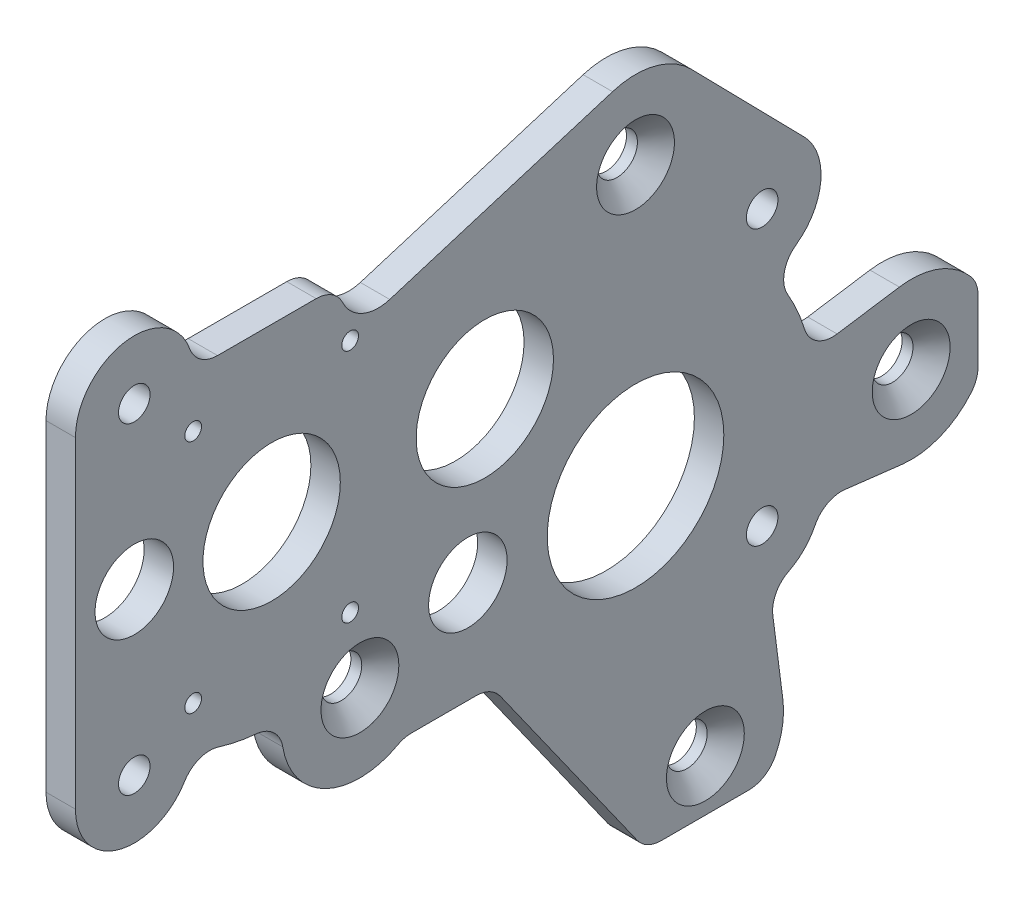
SolidWorks part; units mm, degrees
material "5052-H32"
ref_plane "Front Plane" through (0, 0, 0) normal (0, 0, 1) x (1, 0, 0)
ref_plane "Top Plane" through (0, 0, 0) normal (0, 1, 0) x (1, 0, 0)
ref_plane "Right Plane" through (0, 0, 0) normal (1, 0, 0) x (0, 0, -1)
sketch "Sketch1" plane through (0, 0, 0) normal (1, 0, 0) x (0, 0, -1)
  line L1 (0, 0) -> (146.05, 0)
  line L2 (0, 0) -> (0, 127)
  line L3 (0, 127) -> (146.05, 127)
  line L4 (146.05, 0) -> (146.05, 127)
  dimension "D1" = 146.05
  dimension "D2" = 127
extrude "Boss-Extrude2" add sketch "Sketch1" along normal blind 4.7625
sketch "Sketch2" plane through (4.7625, 0, 0) normal (1, 0, 0) x (0, 0, -1)
  line L0 (66.2432, 127) -> (66.2432, 0) construction
  line L1 (0, 127) -> (0, 0) construction
  line L2 (66.2432, 76.2) -> (90.6336, 51.8096) construction
  line L3 (0, 0) -> (146.05, 0) construction
  line L4 (146.05, 127) -> (0, 127) construction
  circle A0 centre (31.75, 76.2) radius 25.5016 construction
  circle A1 centre (90.6336, 51.8096) radius 8.9916 construction
  circle A2 centre (90.6336, 51.8096) radius 14.2875
  circle A3 centre (31.75, 76.2) radius 11.1125
  circle A4 centre (66.2432, 76.2) radius 25.5016 construction
  circle A5 centre (66.2432, 76.2) radius 8.9916 construction
  circle A6 centre (66.2432, 76.2) radius 11.1125
  dimension "D1" = 51.0032
  dimension "D2" = 17.9832
  dimension "D4" = 28.575
  dimension "D5" = 22.225
  dimension "D6" = 45
  dimension "D3" = 51.0032
  dimension "D7" = 17.9832
  dimension "D8" = 22.225
  dimension "D9" = 31.75
  dimension "D10" = 76.2
extrude "Cut-Extrude1" cut sketch "Sketch2" against normal through all
hole_wizard "CSK for M6 Flat Head Machine Screw1" positions "Sketch3" profile "Sketch4" countersink size "M6" standard "ANSI Metric" end condition through all
sketch "Sketch3" plane through (4.7625, 0, 0) normal (1, 0, 0) x (0, 0, -1)
  circle A1 centre (46.0336, 45.8096) radius 2.5 construction
  circle A2 centre (101.9336, 8.3096) radius 2.5 construction
  circle A3 centre (90.6336, 96.8096) radius 2.5 construction
  circle A4 centre (135.2336, 45.8096) radius 2.5 construction
  circle A5 centre (46.0336, 45.8096) radius 2.5
  circle A6 centre (101.9336, 8.3096) radius 2.5
  circle A7 centre (90.6336, 96.8096) radius 2.5
  circle A8 centre (135.2336, 45.8096) radius 2.5
  point P58 (101.9336, 8.3096)
  point P61 (46.0336, 45.8096)
  point P64 (135.2336, 45.8096)
  point P67 (90.6336, 96.8096)
sketch "Sketch4" plane through (4.7625, 96.8096, -90.6336) normal (0, 1, 0) x (0, 0, -1)
  line L0 (0, 0) -> (0, 4.7625)
  line L1 (0, 4.7625) -> (3.3, 4.7625)
  line L2 (3.3, 4.7625) -> (3.3, 3)
  line L3 (3.3, 3) -> (6.3, 0)
  line L5 (6.3, 0) -> (0, 0)
  line L6 (-3.3, 3) -> (-6.3, 0) construction
  line L11 (0, -6.35) -> (0, 107.95) construction
  dimension "Thru Hole Dia." = 6.6
  dimension "Thru Hole Depth" = 4.7625
  dimension "Near C'Sink Dia." = 12.6
  dimension "Near C'Sink Angle" = 90
hole_wizard "#10 Clearance Hole2" positions "Sketch5" profile "Sketch6" hole size "#10" standard "ANSI Inch" end condition through all
sketch "Sketch5" plane through (4.7625, 0, 0) normal (1, 0, 0) x (0, 0, -1)
  line L2 (9.525, 103.8796) -> (9.525, 51.8096)
  line L6 (0, 127) -> (0, 0) construction
  line L8 (111.125, 35.9346) -> (111.125, 80.3846)
  circle A2 centre (90.6336, 51.8096) radius 14.2875 construction
  point P423 (9.525, 103.8796)
  point P426 (111.125, 80.3846)
  point P432 (9.525, 51.8096)
  point P470 (111.125, 35.9346)
  dimension "D1" = 52.07
  dimension "D2" = 44.45
  dimension "D3" = 101.6
  dimension "D4" = 9.525
  dimension "D5" = 0
  dimension "D6" = 15.875
sketch "Sketch6" plane through (4.7625, 35.9346, -111.125) normal (0, 1, 0) x (0, 0, -1)
  line L0 (0, 0) -> (0, 4.7625)
  line L1 (0, 4.7625) -> (2.5527, 4.7625)
  line L2 (2.5527, 4.7625) -> (2.5527, 0)
  line L5 (2.5527, 0) -> (0, 0)
  line L11 (0, -6.35) -> (0, 107.95) construction
  dimension "Thru Hole Dia." = 5.1054
  dimension "Thru Hole Depth" = 4.7625
fillet "Fillet2" radius 9.525 4 edges at (2.3813, 127, 0) (2.3813, 0, 0) (2.3813, 0, -146.05) (2.3813, 127, -146.05)
hole_wizard "#6-32 Tapped Hole1" positions "Sketch9" profile "Sketch10" tap size "#6-32" standard "ANSI Inch" end condition through all
sketch "Sketch9" plane through (0, 0, 0) normal (-1, 0, 0) x (0, 0, 1)
  line L2 (-44.45, 57.15) -> (-19.05, 57.15)
  line L3 (-44.45, 57.15) -> (-44.45, 95.25)
  line L4 (-44.45, 95.25) -> (-19.05, 95.25)
  line L5 (-19.05, 57.15) -> (-19.05, 95.25)
  line L6 (-44.45, 57.15) -> (-19.05, 95.25) construction
  line L7 (-44.45, 95.25) -> (-19.05, 57.15) construction
  point P17 (-31.75, 76.2)
  point P130 (-19.05, 57.15)
  point P133 (-44.45, 57.15)
  point P136 (-44.45, 95.25)
  point P139 (-19.05, 95.25)
  dimension "D1" = 38.1
  dimension "D2" = 25.4
sketch "Sketch10" plane through (0, 76.2, -31.75) normal (0, 1, 0) x (0, 0, 1)
  line L0 (0, 0) -> (0, 4.7625)
  line L1 (0, 4.7625) -> (1.3525, 4.7625)
  line L2 (1.3525, 4.7625) -> (1.3525, 0)
  line L5 (1.3525, 0) -> (0, 0)
  line L11 (0, -6.35) -> (0, 107.95) construction
  dimension "Thru Tap Drill Dia." = 2.7051
  dimension "Thru Tap Drill Depth" = 4.7625
cosmetic thread "Hole Thread1" parameters "D2"=3.5052
cosmetic thread "Hole Thread2" parameters "D2"=3.5052
cosmetic thread "Hole Thread3" parameters "D2"=3.5052
cosmetic thread "Hole Thread4" parameters "D2"=3.5052
sketch "Sketch11" plane through (4.7625, 0, 0) normal (1, 0, 0) x (0, 0, -1)
  line L0 (19.05, 103.8796) -> (42.6466, 103.8796)
  line L3 (50.8637, 97.8103) -> (86.9141, 108.9004)
  line L4 (117.9243, 87.0551) -> (99.6636, 105.6685)
  line L5 (90.6336, 51.8096) -> (133.328, 58.3153) construction
  line L6 (118.8825, 56.1141) -> (133.328, 58.3153)
  line L7 (111.125, 35.9346) -> (133.7413, 33.2479) construction
  line L9 (111.125, 35.9346) -> (114.4796, 9.928) construction
  line L10 (112.3435, 26.4879) -> (114.4796, 9.928)
  line L14 (91.6113, 0.9971) -> (67.3166, 35.2915)
  line L16 (67.3166, 35.2915) -> (53.0615, 35.2915)
  line L17 (0, 117.475) -> (0, 9.525) construction
  line L18 (0, 51.8096) -> (0, 0)
  line L20 (111.4715, 0) -> (146.05, 0)
  line L21 (9.525, 0) -> (136.525, 0) construction
  line L23 (133.7413, 33.2479) -> (120.5835, 34.811)
  line L24 (146.05, 39.2501) -> (146.05, 0)
  line L25 (146.05, 9.525) -> (146.05, 117.475) construction
  line L27 (146.05, 52.3692) -> (146.05, 127)
  line L28 (146.05, 127) -> (0, 127)
  line L29 (0, 127) -> (0, 103.8796)
  line L30 (136.525, 127) -> (9.525, 127) construction
  line L31 (0, 0) -> (92.3956, 0)
  circle A9 centre (90.6336, 51.8096) radius 28.575 construction
  arc A17 (146.05, 52.3692) -> (146.05, 39.2501) centre (135.2336, 45.8096) ccw construction
  circle A25 centre (90.6336, 96.8096) radius 12.65 construction
  arc A27 (111.4715, 0) -> (92.3956, 0) centre (101.9336, 8.3096) ccw construction
  circle A32 centre (9.525, 77.8446) radius 2.8067 construction
  circle A33 centre (63.5, 51.8096) radius 2.8067 construction
  circle A34 centre (125.057, 77.8446) radius 2.8067 construction
  circle A35 centre (48.9966, 103.8796) radius 2.8067 construction
  circle A36 centre (9.525, 77.8446) radius 2.8067 construction
  circle A37 centre (63.5, 51.8096) radius 2.8067 construction
  circle A38 centre (125.057, 77.8446) radius 2.8067 construction
  circle A39 centre (48.9966, 103.8796) radius 2.8067 construction
  circle A40 centre (9.525, 77.8446) radius 6.35
  arc A41 (42.6466, 103.8796) -> (50.8637, 97.8103) centre (48.9966, 103.8796) ccw
  circle A42 centre (63.5, 51.8096) radius 6.35
  circle A44 centre (46.0336, 45.8096) radius 12.65 construction
  circle A45 centre (31.75, 76.2) radius 28.575 construction
  circle A47 centre (9.525, 103.8796) radius 9.525 construction
  circle A48 centre (9.525, 51.8096) radius 9.525 construction
  circle A49 centre (111.125, 80.3846) radius 9.525 construction
  circle A50 centre (111.125, 35.9346) radius 9.525 construction
  circle A51 centre (90.6336, 96.8096) radius 6.3 construction
  arc A52 (99.6636, 105.6685) -> (86.9141, 108.9004) centre (90.6336, 96.8096) ccw
  arc A53 (117.9243, 87.0551) -> (111.9036, 70.8915) centre (111.125, 80.3846) cw
  arc A54 (118.8825, 56.1141) -> (111.9036, 70.8915) centre (90.6336, 51.8096) ccw
  arc A55 (133.328, 58.3153) -> (146.05, 52.3692) centre (135.2336, 45.8096) cw
  arc A57 (120.5835, 34.811) -> (112.3435, 26.4879) centre (111.125, 35.9346) cw
  circle A58 centre (101.9336, 8.3096) radius 6.3 construction
  arc A59 (91.6113, 0.9971) -> (92.3956, 0) centre (101.9336, 8.3096) ccw
  arc A60 (33.5226, 47.68) -> (53.0615, 35.2915) centre (46.0336, 45.8096) ccw
  circle A61 centre (46.0336, 45.8096) radius 6.3 construction
  arc A62 (33.5226, 47.68) -> (18.9777, 50.6383) centre (31.75, 76.2) cw
  arc A63 (18.9777, 50.6383) -> (0, 51.8096) centre (9.525, 51.8096) cw
  arc A64 (19.05, 103.8796) -> (0, 103.8796) centre (9.525, 103.8796) ccw
  arc A65 (146.05, 39.2501) -> (133.7413, 33.2479) centre (135.2336, 45.8096) cw
  arc A66 (111.4715, 0) -> (114.4796, 9.928) centre (101.9336, 8.3096) ccw
  circle A67 centre (135.2336, 45.8096) radius 6.3 construction
  dimension "D2" = 12.7
  dimension "D3" = 12.7
  dimension "D4" = 12.7
  dimension "D5" = 6.35
  dimension "D9" = 6.35
  dimension "D11" = 6.35
  dimension "D12" = 57.15
  dimension "D7" = 6.35
  dimension "D6" = 19.05
  dimension "D8" = 19.05
  dimension "D10" = 57.15
extrude "Cut-Extrude2" cut sketch "Sketch11" against normal through all
fillet "Fillet28" radius 4.7625 14 edges at (2.3813, 103.8796, -19.05) (2.3813, 103.8796, -42.6466) (2.3813, 70.8915, -111.9036) (2.3813, 56.1141, -118.8825) (2.3813, 39.2501, -146.05) (2.3813, 52.3692, -146.05) (2.3813, 34.811, -120.5835) (2.3813, 26.4879, -112.3435) (2.3813, 0, -111.4715) (2.3813, 0, -92.3956) (2.3813, 35.2915, -67.3166) (2.3813, 35.2915, -53.0615) (2.3813, 47.68, -33.5226) (2.3813, 50.6383, -18.9777)
